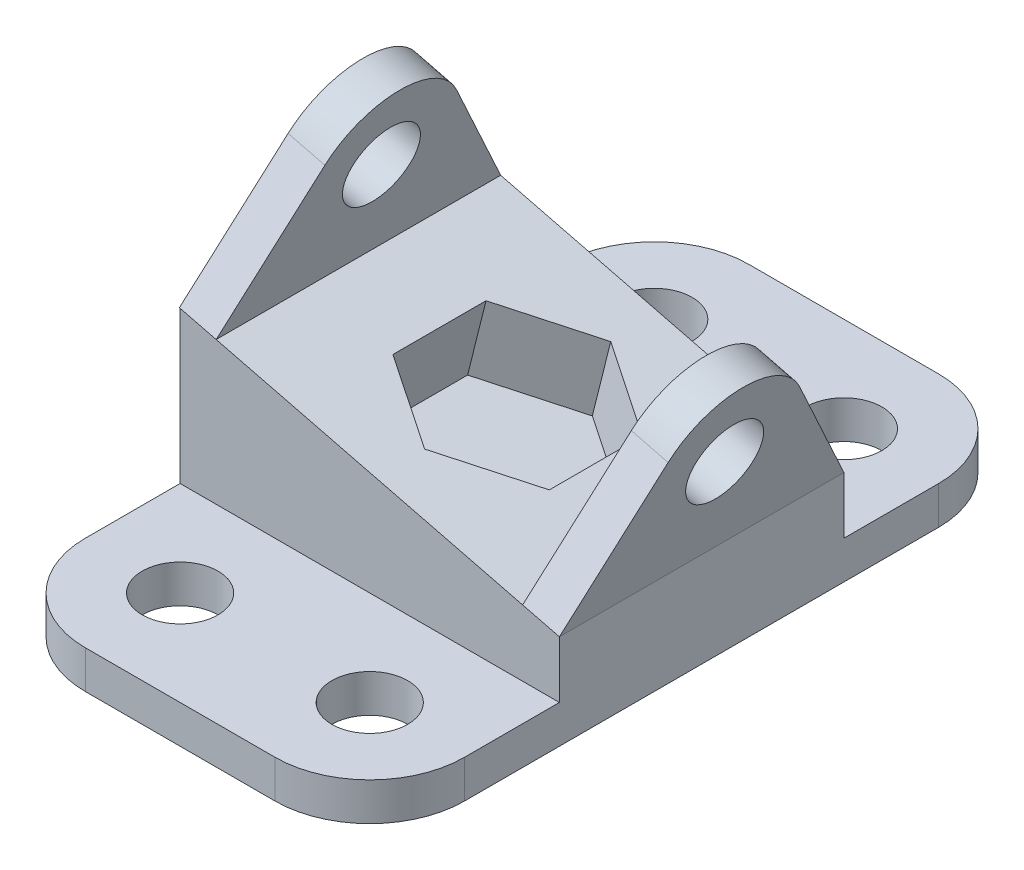
SolidWorks part; units mm, degrees
material "Acero inoxidable al cromo"
ref_plane "Alzado" through (0, 0, 0) normal (0, 0, 1) x (1, 0, 0)
ref_plane "Planta" through (0, 0, 0) normal (0, 1, 0) x (1, 0, 0)
ref_plane "Vista lateral" through (0, 0, 0) normal (1, 0, 0) x (0, 0, -1)
sketch "Croquis1" plane through (0, 0, 0) normal (0, 0, 1) x (1, 0, 0)
  line L0 (0, 0) -> (80, 0)
  line L1 (80, 0) -> (80, 20)
  line L2 (80, 20) -> (0, 40)
  line L3 (0, 40) -> (0, 0)
  dimension "D1" = 80
  dimension "D2" = 40
  dimension "D3" = 20
extrude "Saliente-Extruir1" add sketch "Croquis1" along normal blind 60
sketch "Croquis2" plane through (0, 0, 60) normal (0, 0, 1) x (1, 0, 0)
  line L0 (80, 0) -> (80, 20) construction
  line L1 (0, 0) -> (80, 0)
  line L2 (0, 0) -> (0, 8)
  line L3 (0, 8) -> (80, 8)
  line L4 (80, 0) -> (80, 8)
  dimension "D1" = 8
extrude "Saliente-Extruir2" add sketch "Croquis2" along normal blind 40
ref_plane "Plano1" through (0, 0, 30) normal (0, 0, -1) x (-1, 0, 0)
mirror "Simetría1" about plane through (0, 0, 30) normal (0, 0, -1) of "Saliente-Extruir2"
ref_plane "Plano2" through (70.5882, -17.6471, 0) normal (0.9701, -0.2425, 0) x (0, 0, -1)
sketch "Croquis3" plane through (70.5882, -17.6471, 0) normal (0.9701, -0.2425, 0) x (0, 0, -1)
  line L0 (-30, 38.8057) -> (-30, 58.8057) construction
  line L1 (-60, 38.8057) -> (0, 38.8057) construction
  line L2 (-30, -17.6) -> (-30, 17.6) construction
  line L3 (-60, 38.8057) -> (-43.8612, 66.7974)
  line L4 (0, 38.8057) -> (-16.1388, 66.7974)
  line L5 (-60, 38.8057) -> (0, 38.8057)
  circle A0 centre (-30, 58.8057) radius 16
  circle A1 centre (-30, 58.8057) radius 8
  dimension "D2" = 32
  dimension "D3" = 16
  dimension "D1" = 20
extrude "Saliente-Extruir3" add sketch "Croquis3" against normal blind 8
pattern_linear "MatrizL1" count 2 spacing 74.62 along (-0.9701, 0.2425, 0) of "Saliente-Extruir3"
sketch "Croquis5" plane through (0, 8, 0) normal (0, 1, 0) x (1, 0, 0)
  line L0 (0, 40) -> (0, 0) construction
  line L1 (80, 40) -> (0, 40) construction
  circle A0 centre (20, 20) radius 8
  circle A1 centre (60, 20) radius 8
  circle A2 centre (60, -80) radius 8
  circle A3 centre (20, -80) radius 8
  dimension "D3" = 16
  dimension "D1" = 20
  dimension "D2" = 20
  dimension "D4" = 2
  dimension "D5" = 2
extrude "Cortar-Extruir1" cut sketch "Croquis5" against normal blind 8
fillet "Redondeo2" radius 20 4 edges at (0, 4, 100) (0, 4, -40) (80, 4, -40) (80, 4, 100)
sketch "Croquis6" plane through (9.4118, 37.6471, 0) normal (0.2425, 0.9701, 0) x (0.9701, -0.2425, 0)
  line L0 (64.7607, 0) -> (-1.8593, 0) construction
  line L1 (32.7607, -10.3701) -> (15.7607, -20.185)
  line L2 (15.7607, -20.185) -> (15.7607, -39.815)
  line L3 (15.7607, -39.815) -> (32.7607, -49.6299)
  line L4 (32.7607, -49.6299) -> (49.7607, -39.815)
  line L5 (49.7607, -39.815) -> (49.7607, -20.185)
  line L6 (49.7607, -20.185) -> (32.7607, -10.3701)
  line L8 (72.7607, -60) -> (72.7607, 0) construction
  circle A0 centre (32.7607, -30) radius 17 construction
  dimension "D1" = 34
  dimension "D2" = 30
  dimension "D3" = 40
extrude "Cortar-Extruir2" cut sketch "Croquis6" against normal blind 16
